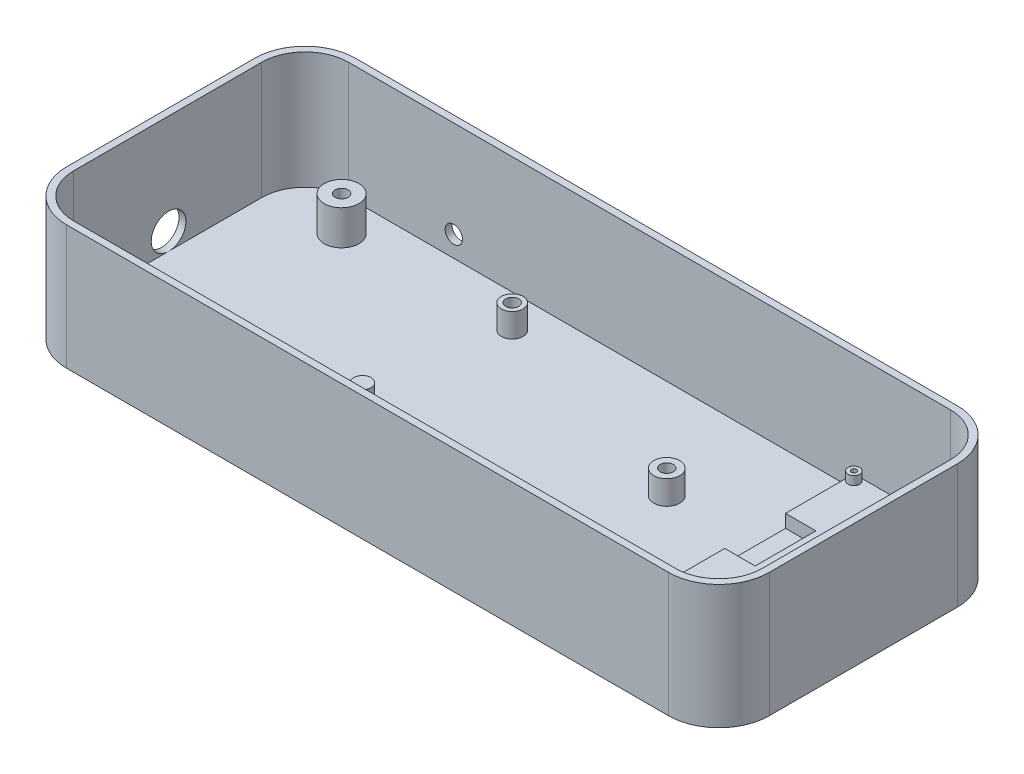
SolidWorks part; units mm, degrees
ref_plane "Front" through (0, 0, 0) normal (0, 0, 1) x (1, 0, 0)
ref_plane "Top" through (0, 0, 0) normal (0, 1, 0) x (1, 0, 0)
ref_plane "Right" through (0, 0, 0) normal (1, 0, 0) x (0, 0, -1)
sketch "Uno Footprint" plane through (0, 0, 0) normal (0, 1, 0) x (1, 0, 0)
  line L1 (-34.3, 26.65) -> (34.3, 26.65)
  line L2 (-34.3, 26.65) -> (-34.3, -26.65)
  line L3 (-34.3, -26.65) -> (34.3, -26.65)
  line L4 (34.3, 26.65) -> (34.3, -26.65)
  line L5 (-34.3, 26.65) -> (34.3, -26.65) construction
  line L6 (-34.3, -26.65) -> (34.3, 26.65) construction
  point P0 (0, 0)
  dimension "D1" = 68.6
  dimension "D2" = 53.3
sketch "Uno Holes" plane through (0, 0, 0) normal (0, 1, 0) x (1, 0, 0)
  line L0 (-34.3, -26.65) -> (34.3, -26.65) construction
  line L1 (-34.3, 26.65) -> (-34.3, -26.65) construction
  circle A0 centre (-19, 24.05) radius 0.8
  circle A1 centre (-20.3, -24.15) radius 0.8
  circle A2 centre (31.8, 8.85) radius 0.8
  circle A3 centre (31.8, -19.05) radius 0.8
  dimension "D1" = 1.6
  dimension "D2" = 1.6
  dimension "D5" = 1.6
  dimension "D9" = 1.6
  dimension "D3" = 2.5
  dimension "D4" = 27.9
  dimension "D6" = 1.3
  dimension "D7" = 14
  dimension "D8" = 50.8
  dimension "D10" = 15.2
  dimension "D11" = 5.1
sketch "Sketch5" plane through (0, 0, 0) normal (0, 1, 0) x (1, 0, 0)
  line L1 (60, 23.75) -> (80, 23.75)
  line L2 (60, 23.75) -> (60, -21.75)
  line L3 (60, -21.75) -> (80, -21.75)
  line L4 (80, 23.75) -> (80, -21.75)
  line L5 (60, 23.75) -> (80, -21.75) construction
  line L6 (60, -21.75) -> (80, 23.75) construction
  circle A0 centre (61.4, 22.35) radius 0.55
  circle A1 centre (78.6, 22.35) radius 0.55
  circle A2 centre (78.6, -20.35) radius 0.55
  circle A3 centre (61.4, -20.35) radius 0.55
  point P0 (70, 1)
  point P7 (70, 1)
  dimension "D1" = 1.1
  dimension "D2" = 1.1
  dimension "D4" = 1.1
  dimension "D5" = 1.1
  dimension "D3" = 45.5
  dimension "D6" = 1.4
  dimension "D7" = 1.4
  dimension "D8" = 1.4
  dimension "D9" = 1.4
  dimension "D10" = 1.4
  dimension "D11" = 1.4
  dimension "D12" = 1.4
  dimension "D13" = 1.4
  dimension "D14" = 70
extrude "Ultrasonic Transducer Base" add sketch "Sketch5" along normal blind 11
sketch "Sketch8" plane through (0, 11, 0) normal (0, 1, 0) x (1, 0, 0)
  line L0 (55.7835, 1) -> (75.2285, 1) construction
  line L1 (60, 1) -> (60, -6)
  line L4 (60, 8) -> (67, 8)
  line L5 (67, 8) -> (67, -6)
  line L6 (67, -6) -> (60, -6)
  line L7 (60, 23.75) -> (60, -21.75) construction
  line L8 (60, 1) -> (60, 8)
  dimension "D4" = 7
extrude "Ultrasonic Pins Cutaway" cut sketch "Sketch8" against normal blind 3
sketch "Standoff Profile" plane through (0, 11, 0) normal (0, -1, 0) x (1, 0, 0)
  line L0 (61.4, 20.35) -> (78.6, -22.35) construction
  line L1 (61.4, -22.35) -> (78.6, 20.35) construction
  circle A0 centre (61.4, 20.35) radius 1.35
  circle A1 centre (78.6, 20.35) radius 1.35
  circle A2 centre (61.4, -22.35) radius 1.35
  circle A3 centre (78.6, -22.35) radius 1.35
  point P2 (70, -1)
  dimension "D1" = 70
  dimension "D2" = 2.7
  dimension "D3" = 2.7
  dimension "D4" = 2.7
  dimension "D5" = 2.7
extrude "Ultrasonic Standoffs" add sketch "Standoff Profile" against normal blind 2
sketch "Sketch6" plane through (0, 11, 0) normal (0, 1, 0) x (1, 0, 0)
  line L0 (61.4, 22.35) -> (78.6, -20.35) construction
  line L1 (61.4, -20.35) -> (78.6, 22.35) construction
  circle A4 centre (61.4, 22.35) radius 0.6
  circle A5 centre (78.6, 22.35) radius 0.6
  circle A6 centre (78.6, -20.35) radius 0.6
  circle A7 centre (61.4, -20.35) radius 0.6
  point P1 (70, 1)
  dimension "D1" = 1.2
  dimension "D2" = 1.2
  dimension "D3" = 1.2
  dimension "D4" = 1.2
  dimension "D5" = 70
sketch "Enclosure Outer Limit" plane through (0, 0, 0) normal (0, 1, 0) x (1, 0, 0)
  line L0 (-74.3, 31.65) -> (-74.3, -31.65)
  line L1 (-74.3, -31.65) -> (84.3, -31.65)
  line L2 (84.3, -31.65) -> (84.3, 31.65)
  line L3 (84.3, 31.65) -> (-74.3, 31.65)
  line L4 (-34.3, 26.65) -> (34.3, 26.65) construction
  line L5 (-34.3, -26.65) -> (34.3, -26.65) construction
  line L6 (-34.3, 26.65) -> (-34.3, -26.65) construction
  line L7 (34.3, 26.65) -> (34.3, -26.65) construction
  dimension "D1" = 5
  dimension "D2" = 5
  dimension "D3" = 40
  dimension "D4" = 50
extrude "Enclosure Base" add sketch "Enclosure Outer Limit" against normal blind 1.6
fillet "Enclosure Fillet" radius 10 4 edges at (84.3, -0.8, -31.65) (84.3, -0.8, 31.65) (-74.3, -0.8, 31.65) (-74.3, -0.8, -31.65)
sketch "Sketch9" plane through (0, 0, 0) normal (0, 1, 0) x (1, 0, 0)
  circle A0 centre (-19, 24.05) radius 2.5
  circle A1 centre (31.8, 8.85) radius 3
  circle A2 centre (31.8, -19.05) radius 3
  circle A3 centre (-20.3, -24.15) radius 2.5
  circle A4 centre (-20.3, -9.15) radius 2
  dimension "D1" = 5
  dimension "D2" = 6
  dimension "D3" = 6
  dimension "D4" = 5
  dimension "D5" = 4
  dimension "D6" = 15
extrude "Uno Standoffs" add sketch "Sketch9" along normal blind 5.5
sketch "Sketch11" plane through (0, 0, 0) normal (0, 1, 0) x (1, 0, 0)
  circle A0 centre (-19, 24.05) radius 1.5
  circle A1 centre (31.8, 8.85) radius 1.5
  circle A2 centre (31.8, -19.05) radius 1.5
  circle A3 centre (-20.3, -24.15) radius 1.5
  dimension "D1" = 3
  dimension "D2" = 3
  dimension "D3" = 3
  dimension "D4" = 3
extrude "Uno Standoff Screw Holes" cut sketch "Sketch11" along normal up to surface (4.5 mm away) from offset 1 up to face at (-19, 5.5, -21.55)
sketch "Sketch12" plane through (0, 0, 0) normal (0, 1, 0) x (1, 0, 0)
  line L4 (84.3, -21.65) -> (84.3, 21.65)
  line L5 (74.3, 31.65) -> (-64.3, 31.65)
  line L6 (-74.3, 21.65) -> (-74.3, -21.65)
  line L7 (-64.3, -31.65) -> (74.3, -31.65)
  line L8 (84.3, -21.65) -> (84.3, 21.65)
  line L9 (74.3, 31.65) -> (-64.3, 31.65)
  line L10 (-74.3, 21.65) -> (-74.3, -21.65)
  line L11 (-64.3, -31.65) -> (74.3, -31.65)
  arc A4 (84.3, 21.65) -> (74.3, 31.65) centre (74.3, 21.65) ccw
  arc A5 (-64.3, 31.65) -> (-74.3, 21.65) centre (-64.3, 21.65) ccw
  arc A6 (-74.3, -21.65) -> (-64.3, -31.65) centre (-64.3, -21.65) ccw
  arc A7 (74.3, -31.65) -> (84.3, -21.65) centre (74.3, -21.65) ccw
  arc A8 (84.3, 21.65) -> (74.3, 31.65) centre (74.3, 21.65) ccw
  arc A9 (-64.3, 31.65) -> (-74.3, 21.65) centre (-64.3, 21.65) ccw
  arc A10 (-74.3, -21.65) -> (-64.3, -31.65) centre (-64.3, -21.65) ccw
  arc A11 (74.3, -31.65) -> (84.3, -21.65) centre (74.3, -21.65) ccw
  dimension "D1" = 0
extrude "Enclosure Wall" add sketch "Sketch12" along normal blind 27 and the other way up to surface (1.6 mm away) thin
sketch "Sketch13" plane through (-75.9, 0, 0) normal (-1, 0, 0) x (0, 0, 1)
  line L0 (-26.65, 0) -> (26.65, 0) construction
  circle A0 centre (-0.2092, 4) radius 4
  dimension "D1" = 8
  dimension "D2" = 4
extrude "LED Ring Cable Hole" cut sketch "Sketch13" against normal up to surface (1.6 mm away) up to face at (-74.3, 13.5, 0)
sketch "Sketch14" plane through (0, 0, 0) normal (0, 1, 0) x (1, 0, 0)
  line L0 (-64.3, -31.65) -> (74.3, -31.65) construction
  line L1 (-75.9, 21.65) -> (-75.9, -21.65) construction
  line L2 (74.3, 31.65) -> (-64.3, 31.65) construction
  circle A0 centre (-57.9, 23.65) radius 4
  circle A1 centre (-57.9, -23.65) radius 4
  dimension "D5" = 8
  dimension "D6" = 8
  dimension "D1" = 8
  dimension "D2" = 18
  dimension "D3" = 8
  dimension "D4" = 18
extrude "Bus Screw Posts" add sketch "Sketch14" along normal blind 8
sketch "Sketch15" plane through (0, 8, 0) normal (0, 1, 0) x (1, 0, 0)
  circle A0 centre (-57.9, 23.65) radius 1.5
  circle A1 centre (-57.9, -23.65) radius 1.5
  dimension "D1" = 3
  dimension "D2" = 3
extrude "Bus Screw Holes" cut sketch "Sketch15" against normal blind 6
sketch "Sketch16" plane through (0, 0, -33.25) normal (0, 0, -1) x (-1, 0, 0)
  circle A0 centre (40.0573, 4.801) radius 2
  dimension "D1" = 4
extrude "Power Cord Hole" cut sketch "Sketch16" against normal up to surface (1.6 mm away) up to face at (5, 13.5, -31.65)
fillet "Fillet1" radius 1.5 4 edges at (60, 5.5, 21.75) (80, 5.5, -23.75) (60, 5.5, -23.75) (80, 5.5, 21.75)
extrude "Cut Pin Holes" cut sketch "Sketch6" along normal blind 10
sketch "Sketch17" plane through (0, 0, 0) normal (0, 1, 0) x (1, 0, 0)
  line L0 (78.6, 22.35) -> (78.6, -20.35) construction
  line L1 (78.6, -20.35) -> (61.4, -20.35) construction
  line L2 (85.9, -21.65) -> (85.9, 21.65) construction
  line L3 (-64.3, -33.25) -> (74.3, -33.25) construction
  dimension "D1" = 7.3
  dimension "D2" = 17.2
  dimension "D3" = 12.9
